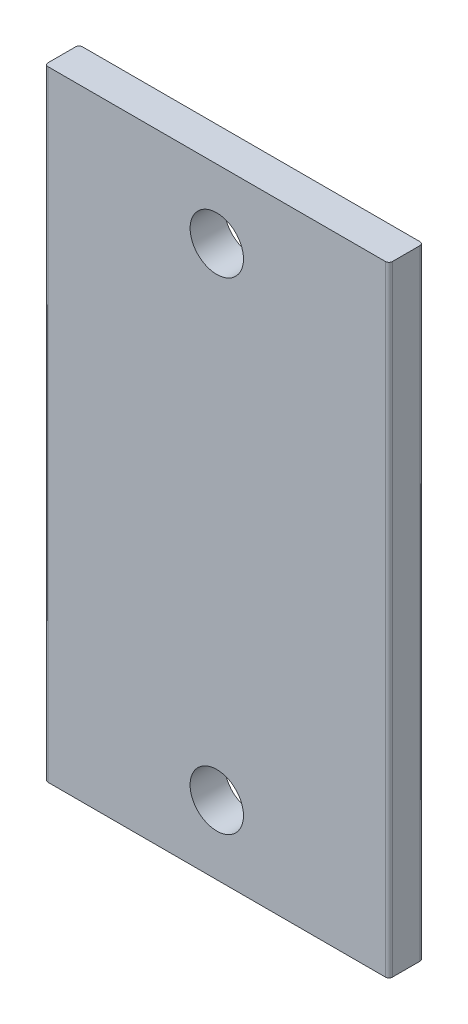
SolidWorks part; units mm, degrees
ref_plane "Plan de face" through (0, 0, 0) normal (0, 0, 1) x (1, 0, 0)
ref_plane "Plan de dessus" through (0, 0, 0) normal (0, 1, 0) x (1, 0, 0)
ref_plane "Plan de droite" through (0, 0, 0) normal (1, 0, 0) x (0, 0, -1)
sketch "Esquisse1" plane through (0, 0, 0) normal (0, 0, 1) x (1, 0, 0)
  line L5 (-50, -90) -> (50, -90)
  line L6 (-50, -90) -> (-50, 90)
  line L7 (-50, 90) -> (50, 90)
  line L8 (50, -90) -> (50, 90)
  line L9 (-50, -90) -> (50, 90) construction
  line L10 (-50, 90) -> (50, -90) construction
  point P0 (0, 0)
  point P9 (0, 0)
  dimension "D1" = 100
  dimension "D2" = 180
extrude "Boss.-Extru.1" add sketch "Esquisse1" along normal blind 10
hole_wizard "M14 Clearance Hole1" positions "Sketch1" profile "Sketch2" hole size "M14" standard "ISO" end condition up to next
sketch "Sketch1" plane through (0, 0, 10) normal (0, 0, 1) x (1, 0, 0)
  line L1 (0, 70) -> (0, -70) construction
  line L6 (-50, 90) -> (-50, -90) construction
  point P0 (0, 70)
  point P7 (0, -70)
  point P13 (0, 0)
  point P25 (60, -70)
  point P26 (60, 70)
  dimension "D3" = 50
  dimension "D4" = 140
  dimension "D1" = 2
  dimension "D2" = 2
sketch "Sketch2" plane through (0, 70, 10) normal (1, 0, 0) x (0, -1, 0)
  line L0 (0, 0) -> (0, 10)
  line L1 (0, 10) -> (7.75, 10)
  line L2 (7.75, 10) -> (7.75, 0)
  line L5 (7.75, 0) -> (0, 0)
  line L11 (0, -6.35) -> (0, 107.95) construction
  dimension "Diámetro de taladro hasta el siguiente" = 15.5
  dimension "Profundidad de taladro hasta el siguiente" = 10
fillet "Fillet1" radius 1 4 edges at (50, 0, 0) (50, 0, 10) (-50, 0, 0) (-50, 0, 10)
